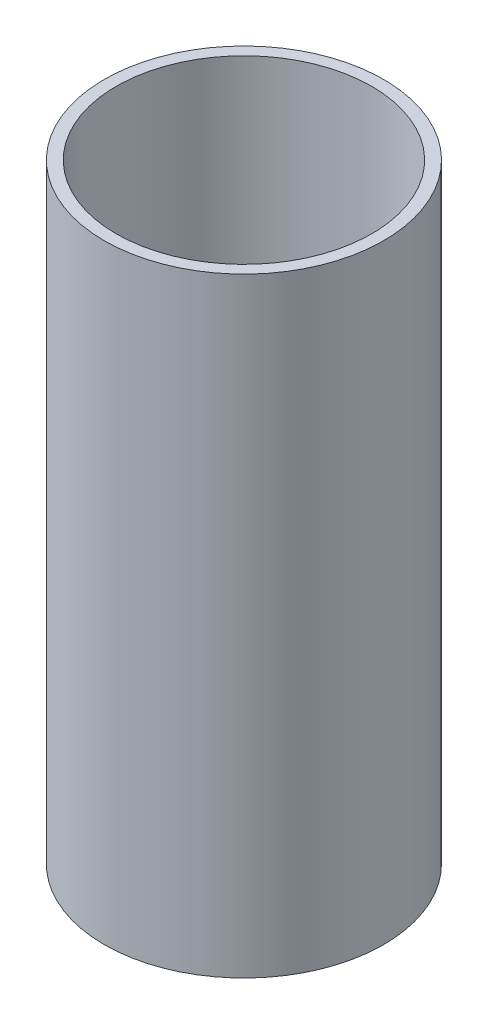
SolidWorks part; units mm, degrees
material "6061-T6 (SS)"
ref_plane "Front Plane" through (0, 0, 0) normal (0, 0, 1) x (1, 0, 0)
ref_plane "Top Plane" through (0, 0, 0) normal (0, 1, 0) x (1, 0, 0)
ref_plane "Right Plane" through (0, 0, 0) normal (1, 0, 0) x (0, 0, -1)
sketch "Sketch1" plane through (0, 0, 0) normal (0, 1, 0) x (1, 0, 0)
  circle A0 centre (0, 0) radius 69.85
  circle A1 centre (0, 0) radius 63.881
  dimension "D1" = 139.7
  dimension "D2" = 127.762
extrude "Boss-Extrude1" add sketch "Sketch1" along normal blind 304.8
